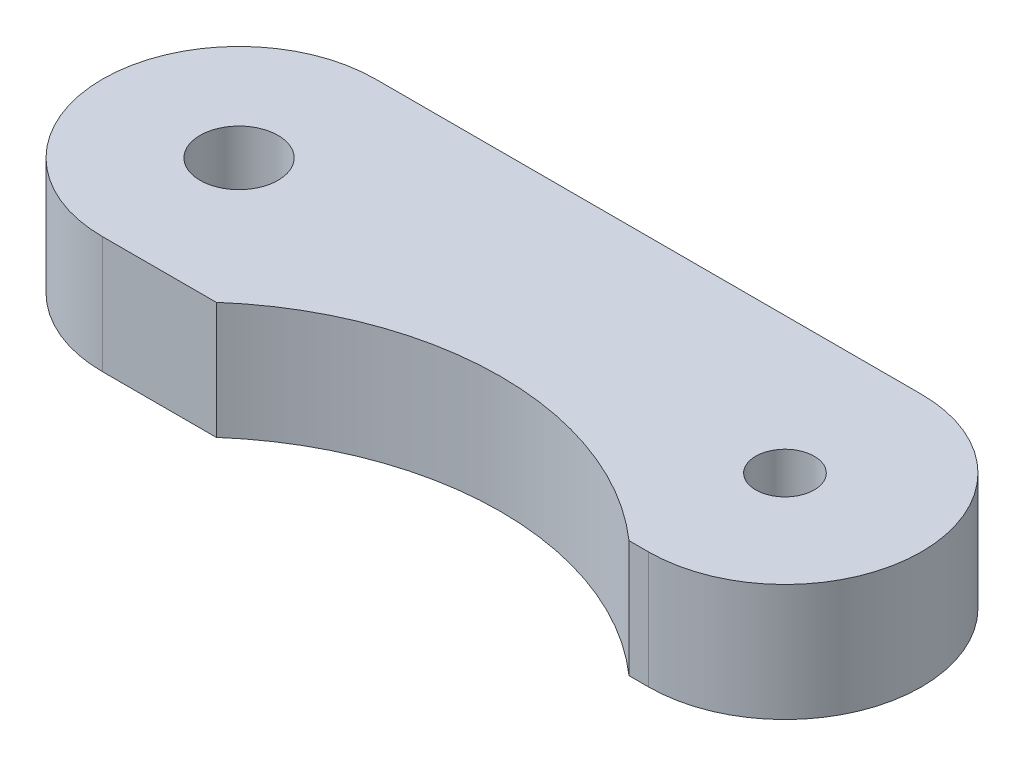
SolidWorks part; units mm, degrees
ref_plane "Front Plane" through (0, 0, 0) normal (0, 0, 1) x (1, 0, 0)
ref_plane "Top Plane" through (0, 0, 0) normal (0, 1, 0) x (1, 0, 0)
ref_plane "Right Plane" through (0, 0, 0) normal (1, 0, 0) x (0, 0, -1)
sketch "Sketch1" plane through (0, 0, 0) normal (0, 1, 0) x (1, 0, 0)
  line L0 (0, 0) -> (14, 0) construction
  line L1 (0, 3.5) -> (14, 3.5)
  line L2 (0, -3.5) -> (14, -3.5)
  arc A0 (0, 3.5) -> (0, -3.5) centre (0, 0) ccw
  arc A1 (14, -3.5) -> (14, 3.5) centre (14, 0) ccw
  circle A2 centre (14, 0) radius 0.75
  circle A3 centre (0, 0) radius 1
  point P3 (7, 0)
  dimension "D2" = 2
  dimension "D3" = 1.5
  dimension "D4" = 3.5
  dimension "D1" = 14
extrude "Boss-Extrude1" add sketch "Sketch1" along normal blind 3
sketch "Sketch2" plane through (0, 3, 0) normal (0, 1, 0) x (1, 0, 0)
  line L0 (0, -3.5) -> (14, -3.5) construction
  line L1 (2.917, -3.5) -> (13.5, -3.5)
  arc A0 (2.917, -3.5) -> (13.5, -3.5) centre (8.2085, -9.5) cw
  dimension "D2" = 8
  dimension "D3" = 6
  dimension "D1" = 0.5
extrude "Cut-Extrude1" cut sketch "Sketch2" against normal blind 10
